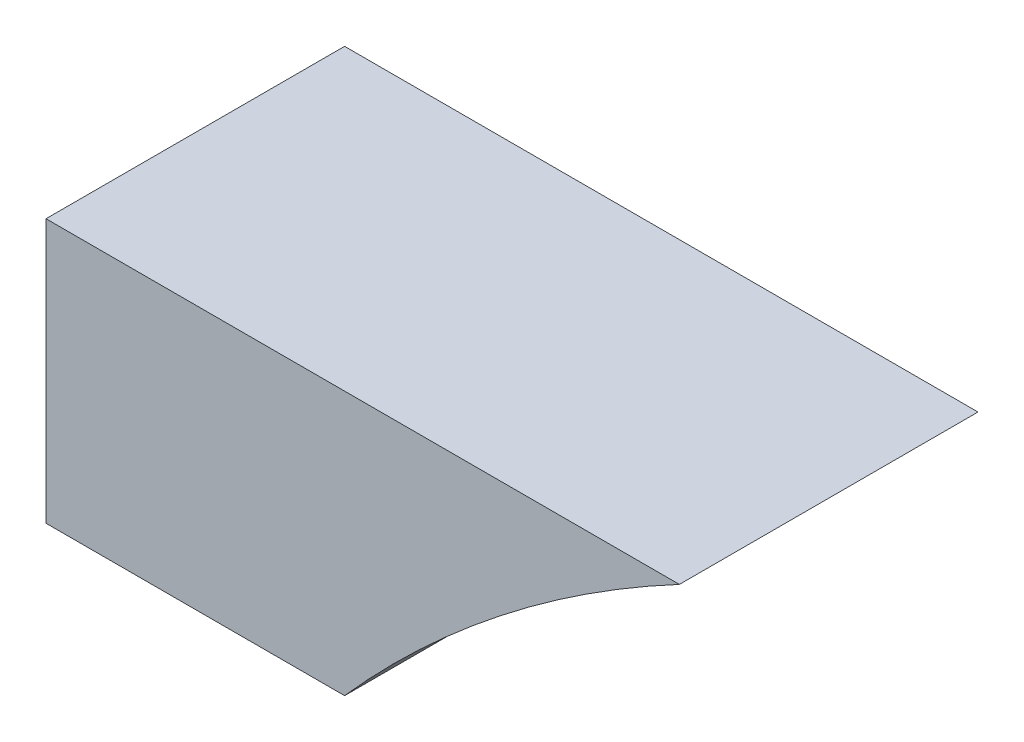
SolidWorks part; units mm, degrees
material "砖"
ref_plane "前视基准面" through (0, 0, 0) normal (0, 0, 1) x (1, 0, 0)
ref_plane "上视基准面" through (0, 0, 0) normal (0, 1, 0) x (1, 0, 0)
ref_plane "右视基准面" through (0, 0, 0) normal (1, 0, 0) x (0, 0, -1)
sketch "草图1" plane through (0, 0, 0) normal (0, 0, 1) x (1, 0, 0)
  line L0 (-4560, 0) -> (-7920, 0)
  line L1 (-12480, 7680) -> (0, 7680)
  line L2 (-12480, 7680) -> (-12480, 0)
  line L3 (-12480, 0) -> (0, 0)
  line L4 (0, 7680) -> (0, 0)
  line L5 (-7920, 0) -> (-7920, 3840)
  line L6 (-7920, 3840) -> (-4560, 3840)
  line L7 (-4560, 3840) -> (-4560, 0)
  line L8 (-7920, 3840) -> (-8160, 3840)
  line L9 (-4560, 3840) -> (-4320, 3840)
  line L10 (-7837.7749, 4359.1486) -> (-8066.0285, 4433.3126)
  line L11 (-7599.1486, 4827.4792) -> (-7793.3126, 4968.5477)
  line L12 (-7227.4792, 5199.1486) -> (-7368.5477, 5393.3126)
  line L13 (-6759.1486, 5437.7749) -> (-6833.3126, 5666.0285)
  line L14 (-6240, 5520) -> (-6240, 5760)
  line L15 (-5720.8514, 5437.7749) -> (-5646.6874, 5666.0285)
  line L16 (-5252.5208, 5199.1486) -> (-5111.4523, 5393.3126)
  line L17 (-4880.8514, 4827.4792) -> (-4686.6874, 4968.5477)
  line L18 (-4642.2251, 4359.1486) -> (-4413.9715, 4433.3126)
  line L19 (-4560, 3840) -> (-4320, 3840)
  line L20 (-4573.7633, 3298.6069) -> (-4560, 3294.1349)
  line L21 (-6833.3126, 5666.0285) -> (-6928.8298, 5960)
  line L22 (-5683.7694, 5551.9017) -> (-5551.1702, 5960)
  line L23 (-5551.1702, 5960) -> (-6928.8298, 5960)
  line L24 (-7920, 0) -> (-9123.3069, 0)
  line L25 (-8160, 0) -> (-8640, 0)
  line L26 (-8160, 0) -> (-8640, 0)
  line L27 (-8640, 3840) -> (-8160, 3840)
  line L28 (-8640, 3840) -> (-8640, 4264)
  line L29 (-7837.7749, 3320.8514) -> (-7920, 3294.1349) [skipped]
  line L30 (-7599.1486, 2852.5208) -> (-7793.3126, 2711.4523) [skipped]
  line L31 (-7227.4792, 2480.8514) -> (-7368.5477, 2286.6874) [skipped]
  line L32 (-6759.1486, 2242.2251) -> (-6833.3126, 2013.9715) [skipped]
  line L33 (-6240, 2160) -> (-6240, 1920) [skipped]
  line L34 (-5720.8514, 2242.2251) -> (-5646.6874, 2013.9715) [skipped]
  line L35 (-5252.5208, 2480.8514) -> (-5111.4523, 2286.6874) [skipped]
  line L36 (-4880.8514, 2852.5208) -> (-4686.6874, 2711.4523) [skipped]
  line L37 (-8640, 4264) -> (-8112.5982, 4264)
  line L38 (-8112.5982, 4264) -> (-8592.5982, 4264)
  line L39 (-8592.5982, 4264) -> (-8592.5982, 4688)
  line L40 (-8592.5982, 4688) -> (-7962.5841, 4688)
  line L41 (-7962.5841, 4688) -> (-8442.5841, 4688)
  line L42 (-8442.5841, 4688) -> (-8442.5841, 5112)
  line L43 (-8442.5841, 5112) -> (-7678.1989, 5112)
  line L44 (-7678.1989, 5112) -> (-8158.1989, 5112)
  line L45 (-8158.1989, 5112) -> (-8158.1989, 5536)
  line L46 (-8158.1989, 5536) -> (-7139.9911, 5536)
  line L47 (-7139.9911, 5536) -> (-7619.9911, 5536)
  line L48 (-7619.9911, 5536) -> (-7619.9911, 5960)
  line L49 (-7619.9911, 5960) -> (-6928.8298, 5960)
  arc A0 (-4560, 3840) -> (-7920, 3840) centre (-6240, 3840) ccw
  arc A1 (-4320, 3840) -> (-8160, 3840) centre (-6240, 3840) ccw
  point P7 (-6240, 0)
  point P56 (-6240, 3840)
  dimension "D5" = 3840
  dimension "D1" = 12480
  dimension "D2" = 7680
  dimension "D3" = 3360
  dimension "D4" = 3840
  dimension "D7" = 240
  dimension "D8" = 480
  dimension "D9" = 424
  dimension "D10" = 720
  dimension "D11" = 480
  dimension "D12" = 480
  dimension "D13" = 480
  dimension "D14" = 480
  dimension "D6" = 20
extrude "凸台-拉伸1" add sketch "草图1" along normal blind 480 contours A1 L46 L45 L43
scale "缩放比例1" scale about origin uniform scaling yes scale factor 1.3
